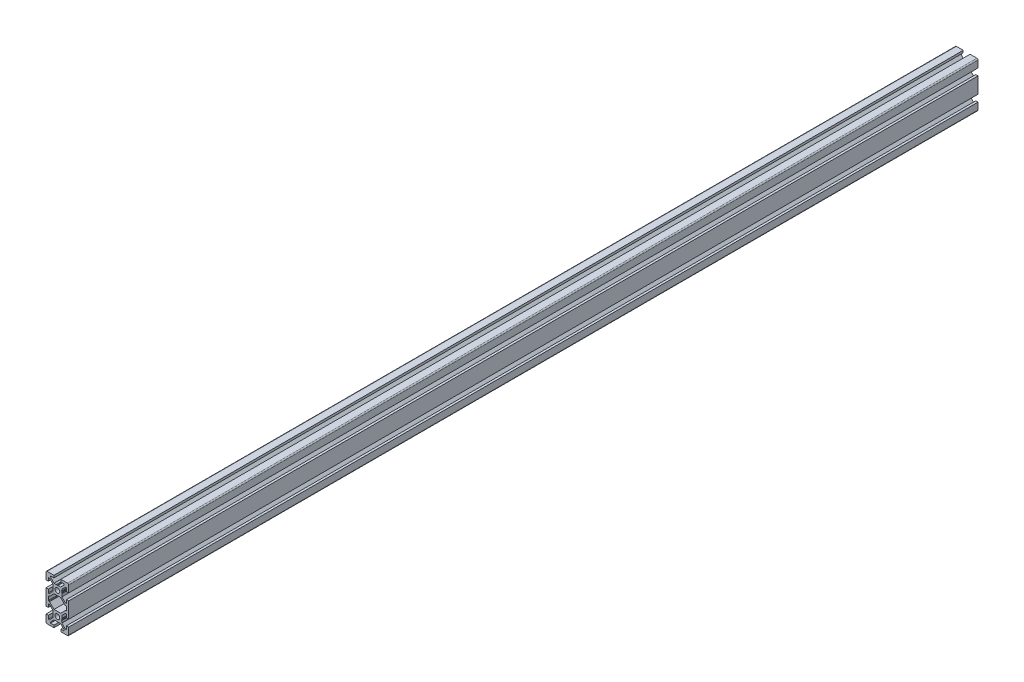
SolidWorks part; units mm, degrees
ref_plane "Front Plane" through (0, 0, 0) normal (0, 0, 1) x (1, 0, 0)
ref_plane "Top Plane" through (0, 0, 0) normal (0, 1, 0) x (1, 0, 0)
ref_plane "Right Plane" through (0, 0, 0) normal (1, 0, 0) x (0, 0, -1)
ref_plane "Plane1" through (0, 0, -600) normal (0, 0, -1) x (-1, 0, 0)
sketch "Sketch1" plane through (0, 0, -600) normal (0, 0, -1) x (-1, 0, 0)
  line L0 (8, 1.7) -> (8, -1.7)
  line L1 (7.7, -2) -> (7.0636, -2)
  line L2 (6.8515, -2.0879) -> (2.9393, -6)
  line L3 (2.9393, -6) -> (-2.9393, -6)
  line L4 (-2.9393, -6) -> (-6.8515, -2.0879)
  line L5 (-7.0636, -2) -> (-7.7, -2)
  line L6 (-8, -1.7) -> (-8, 1.7)
  line L7 (-7.7, 2) -> (-7.0636, 2)
  line L8 (-6.8515, 2.0879) -> (-2.9393, 6)
  line L9 (-2.9393, 6) -> (2.9393, 6)
  line L10 (2.9393, 6) -> (6.8515, 2.0879)
  line L11 (7.0636, 2) -> (7.7, 2)
  line L12 (10, -7) -> (10, 7)
  line L13 (10, 7) -> (8, 7)
  line L14 (8, 7) -> (8, 4)
  line L15 (8, 4) -> (7.0607, 4)
  line L16 (7.0607, 4) -> (4, 7.0607)
  line L17 (4, 7.0607) -> (4, 7.5)
  line L18 (4, 7.5) -> (3.751, 8.7811)
  line L19 (3.751, 8.7811) -> (3.933, 9.0964)
  line L20 (3.933, 9.5964) -> (3.7, 10)
  line L21 (3.7, 10) -> (3.933, 10.4036)
  line L22 (4, 10.6536) -> (4, 12.9393)
  line L23 (4, 12.9393) -> (7.0607, 16)
  line L24 (7.0607, 16) -> (8, 16)
  line L25 (8, 16) -> (8, 13)
  line L26 (8, 13) -> (10, 13)
  line L27 (10, 13) -> (10, 19)
  line L28 (9, 20) -> (3, 20)
  line L29 (3, 20) -> (3, 18)
  line L30 (3, 18) -> (6, 18)
  line L31 (6, 18) -> (6, 17.0607)
  line L32 (6, 17.0607) -> (2.9393, 14)
  line L33 (2.9393, 14) -> (2.5, 14)
  line L34 (2.5, 14) -> (1.2189, 13.751)
  line L35 (1.2189, 13.751) -> (0.9036, 13.933)
  line L36 (0.4036, 13.933) -> (0, 13.7)
  line L37 (0, 13.7) -> (-0.4036, 13.933)
  line L38 (-0.6536, 14) -> (-2.9393, 14)
  line L39 (-2.9393, 14) -> (-6, 17.0607)
  line L40 (-6, 17.0607) -> (-6, 18)
  line L41 (-6, 18) -> (-3, 18)
  line L42 (-3, 18) -> (-3, 20)
  line L43 (-3, 20) -> (-9, 20)
  line L44 (-10, 19) -> (-10, 13)
  line L45 (-10, 13) -> (-8, 13)
  line L46 (-8, 13) -> (-8, 16)
  line L47 (-8, 16) -> (-7.0607, 16)
  line L48 (-7.0607, 16) -> (-4, 12.9393)
  line L49 (-4, 12.9393) -> (-4, 12.5)
  line L50 (-4, 12.5) -> (-3.751, 11.2189)
  line L51 (-3.751, 11.2189) -> (-3.933, 10.9036)
  line L52 (-3.933, 10.4036) -> (-3.7, 10)
  line L53 (-3.7, 10) -> (-3.933, 9.5964)
  line L54 (-4, 9.3464) -> (-4, 7.0607)
  line L55 (-4, 7.0607) -> (-7.0607, 4)
  line L56 (-7.0607, 4) -> (-8, 4)
  line L57 (-8, 4) -> (-8, 7)
  line L58 (-8, 7) -> (-10, 7)
  line L59 (-10, 7) -> (-10, -7)
  line L60 (-10, -7) -> (-8, -7)
  line L61 (-8, -7) -> (-8, -4)
  line L62 (-8, -4) -> (-7.0607, -4)
  line L63 (-7.0607, -4) -> (-4, -7.0607)
  line L64 (-4, -7.0607) -> (-4, -9.3464)
  line L65 (-3.933, -9.5964) -> (-3.7, -10)
  line L66 (-3.7, -10) -> (-3.933, -10.4036)
  line L67 (-3.933, -10.9036) -> (-3.751, -11.2189)
  line L68 (-3.751, -11.2189) -> (-4, -12.5)
  line L69 (-4, -12.5) -> (-4, -12.9393)
  line L70 (-4, -12.9393) -> (-7.0607, -16)
  line L71 (-7.0607, -16) -> (-8, -16)
  line L72 (-8, -16) -> (-8, -13)
  line L73 (-8, -13) -> (-10, -13)
  line L74 (-10, -13) -> (-10, -19)
  line L75 (-9, -20) -> (-3, -20)
  line L76 (-3, -20) -> (-3, -18)
  line L77 (-3, -18) -> (-6, -18)
  line L78 (-6, -18) -> (-6, -17.0607)
  line L79 (-6, -17.0607) -> (-2.9393, -14)
  line L80 (-2.9393, -14) -> (-0.6536, -14)
  line L81 (-0.4036, -13.933) -> (0, -13.7)
  line L82 (0, -13.7) -> (0.4036, -13.933)
  line L83 (0.9036, -13.933) -> (1.2189, -13.751)
  line L84 (1.2189, -13.751) -> (2.5, -14)
  line L85 (2.5, -14) -> (2.9393, -14)
  line L86 (2.9393, -14) -> (6, -17.0607)
  line L87 (6, -17.0607) -> (6, -18)
  line L88 (6, -18) -> (3, -18)
  line L89 (3, -18) -> (3, -20)
  line L90 (3, -20) -> (9, -20)
  line L91 (10, -19) -> (10, -13)
  line L92 (10, -13) -> (8, -13)
  line L93 (8, -13) -> (8, -16)
  line L94 (8, -16) -> (7.0607, -16)
  line L95 (7.0607, -16) -> (4, -12.9393)
  line L96 (4, -12.9393) -> (4, -10.6536)
  line L97 (3.933, -10.4036) -> (3.7, -10)
  line L98 (3.7, -10) -> (3.933, -9.5964)
  line L99 (3.933, -9.0964) -> (3.751, -8.7811)
  line L100 (3.751, -8.7811) -> (4, -7.5)
  line L101 (4, -7.5) -> (4, -7.0607)
  line L102 (4, -7.0607) -> (7.0607, -4)
  line L103 (7.0607, -4) -> (8, -4)
  line L104 (8, -4) -> (8, -7)
  line L105 (8, -7) -> (10, -7)
  circle A0 centre (0, -10) radius 2.1
  circle A1 centre (0, 10) radius 2.1
  arc A2 (7.7, 2) -> (8, 1.7) centre (7.7, 1.7) cw
  arc A3 (8, -1.7) -> (7.7, -2) centre (7.7, -1.7) cw
  arc A4 (7.0636, -2) -> (6.8515, -2.0879) centre (7.0636, -2.3) ccw
  arc A5 (-6.8515, -2.0879) -> (-7.0636, -2) centre (-7.0636, -2.3) ccw
  arc A6 (-7.7, -2) -> (-8, -1.7) centre (-7.7, -1.7) cw
  arc A7 (-8, 1.7) -> (-7.7, 2) centre (-7.7, 1.7) cw
  arc A8 (-7.0636, 2) -> (-6.8515, 2.0879) centre (-7.0636, 2.3) ccw
  arc A9 (6.8515, 2.0879) -> (7.0636, 2) centre (7.0636, 2.3) ccw
  arc A10 (3.933, 9.0964) -> (3.933, 9.5964) centre (3.5, 9.3464) ccw
  arc A11 (3.933, 10.4036) -> (4, 10.6536) centre (3.5, 10.6536) ccw
  arc A12 (10, 19) -> (9, 20) centre (9, 19) ccw
  arc A13 (0.9036, 13.933) -> (0.4036, 13.933) centre (0.6536, 13.5) ccw
  arc A14 (-0.4036, 13.933) -> (-0.6536, 14) centre (-0.6536, 13.5) ccw
  arc A15 (-9, 20) -> (-10, 19) centre (-9, 19) ccw
  arc A16 (-3.933, 10.9036) -> (-3.933, 10.4036) centre (-3.5, 10.6536) ccw
  arc A17 (-3.933, 9.5964) -> (-4, 9.3464) centre (-3.5, 9.3464) ccw
  arc A18 (-4, -9.3464) -> (-3.933, -9.5964) centre (-3.5, -9.3464) ccw
  arc A19 (-3.933, -10.4036) -> (-3.933, -10.9036) centre (-3.5, -10.6536) ccw
  arc A20 (-10, -19) -> (-9, -20) centre (-9, -19) ccw
  arc A21 (-0.6536, -14) -> (-0.4036, -13.933) centre (-0.6536, -13.5) ccw
  arc A22 (0.4036, -13.933) -> (0.9036, -13.933) centre (0.6536, -13.5) ccw
  arc A23 (9, -20) -> (10, -19) centre (9, -19) ccw
  arc A24 (4, -10.6536) -> (3.933, -10.4036) centre (3.5, -10.6536) ccw
  arc A25 (3.933, -9.5964) -> (3.933, -9.0964) centre (3.5, -9.3464) ccw
  dimension "D1" = 4.2
  dimension "D3" = 0.3
  dimension "D4" = 0.3
  dimension "D5" = 0.3
  dimension "D6" = 0.3
  dimension "D7" = 0.3
  dimension "D8" = 0.3
  dimension "D9" = 0.3
  dimension "D10" = 0.5
  dimension "D11" = 0.5
  dimension "D12" = 1
  dimension "D13" = 0.5
  dimension "D14" = 0.5
  dimension "D15" = 1
  dimension "D16" = 0.5
  dimension "D17" = 0.5
  dimension "D18" = 0.5
  dimension "D19" = 0.5
  dimension "D20" = 0.4036
  dimension "D21" = 0.5
  dimension "D22" = 0.5
  dimension "D23" = 1
  dimension "D24" = 0.5
  dimension "D25" = 0.5
  dimension "D26" = 0.4036
  dimension "D27" = 0.6536
  dimension "D28" = 0.6536
  dimension "D29" = 0.9036
  dimension "D30" = 0.9036
  dimension "D31" = 1.2189
  dimension "D32" = 1.2189
  dimension "D33" = 2.5
  dimension "D34" = 2.5
  dimension "D35" = 2.9393
  dimension "D36" = 2.9393
  dimension "D37" = 3
  dimension "D38" = 3.5
  dimension "D39" = 6
  dimension "D40" = 6.8515
  dimension "D41" = 3.7
  dimension "D42" = 3.7
  dimension "D43" = 3.751
  dimension "D44" = 3.751
  dimension "D45" = 3.933
  dimension "D46" = 3.933
  dimension "D47" = 6.8515
  dimension "D48" = 7.0607
  dimension "D49" = 7.0607
  dimension "D50" = 7.0636
  dimension "D51" = 7.0636
  dimension "D52" = 8
  dimension "D53" = 10
  dimension "D54" = 3
  dimension "D55" = 4
  dimension "D56" = 6
  dimension "D57" = 6.8515
  dimension "D58" = 6.8515
  dimension "D59" = 7.0607
  dimension "D60" = 7.0607
  dimension "D61" = 0.4036
  dimension "D62" = 0.4036
  dimension "D63" = 0.6536
  dimension "D64" = 0.6536
  dimension "D65" = 2.9393
  dimension "D66" = 2.9393
  dimension "D67" = 8
  dimension "D68" = 2
  dimension "D69" = 3.5
  dimension "D70" = 3.5
  dimension "D71" = 3.7
  dimension "D72" = 3.7
  dimension "D73" = 3.751
  dimension "D74" = 3.751
  dimension "D75" = 3.933
  dimension "D76" = 3.933
  dimension "D77" = 4
  dimension "D78" = 6
  dimension "D79" = 7
  dimension "D80" = 7.0607
  dimension "D81" = 7.0607
  dimension "D82" = 7.5
  dimension "D83" = 8.7811
  dimension "D84" = 9.0964
  dimension "D85" = 9.3464
  dimension "D86" = 9.3464
  dimension "D87" = 9.5964
  dimension "D88" = 9.5964
  dimension "D89" = 10.4036
  dimension "D90" = 12.5
  dimension "D91" = 13
  dimension "D92" = 13.5
  dimension "D93" = 13.5
  dimension "D94" = 18
  dimension "D95" = 20
  dimension "D96" = 2
  dimension "D97" = 4
  dimension "D98" = 6
  dimension "D99" = 7
  dimension "D100" = 7.0607
  dimension "D101" = 7.0607
  dimension "D102" = 7.5
  dimension "D103" = 8.7811
  dimension "D104" = 9.0964
  dimension "D105" = 9.3464
  dimension "D106" = 9.3464
  dimension "D107" = 9.5964
  dimension "D108" = 9.5964
  dimension "D109" = 10.4036
  dimension "D110" = 12.5
  dimension "D111" = 13
  dimension "D112" = 18
extrude "Boss-Extrude1" add sketch "Sketch1" against normal blind 800
